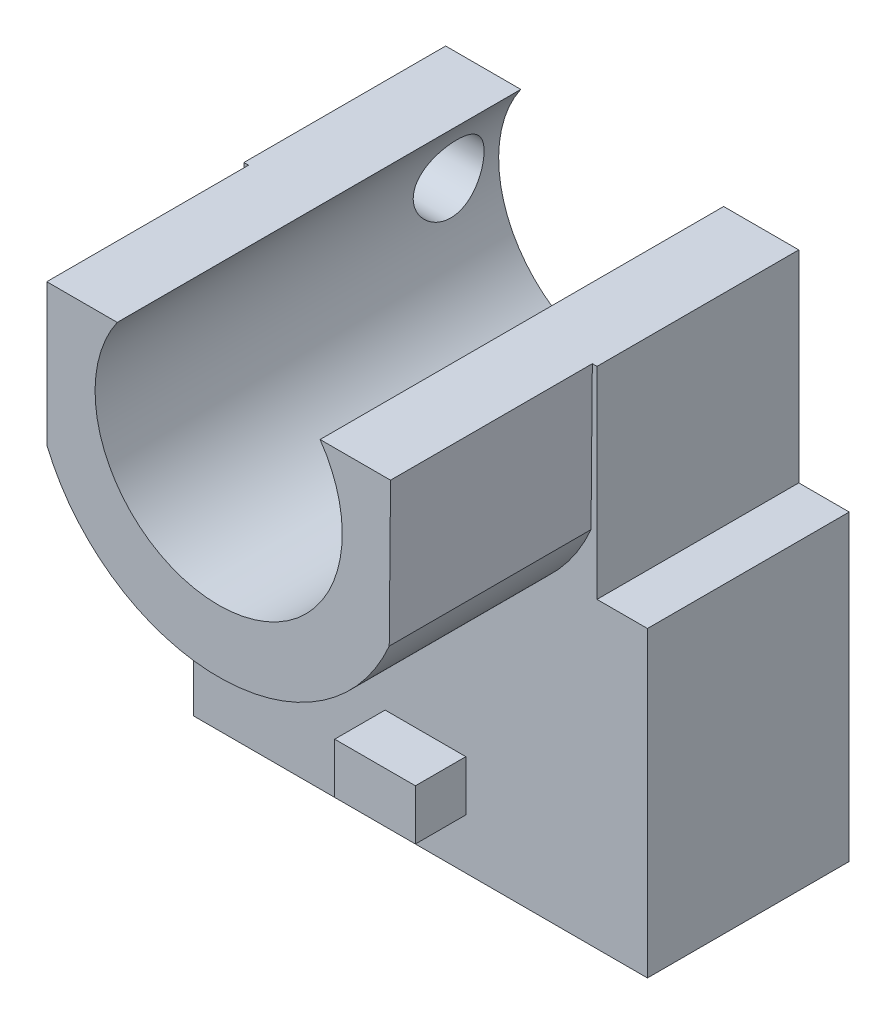
SolidWorks part; units mm, degrees
ref_plane "Front Plane" through (0, 0, 0) normal (0, 0, 1) x (1, 0, 0)
ref_plane "Top Plane" through (0, 0, 0) normal (0, 1, 0) x (1, 0, 0)
ref_plane "Right Plane" through (0, 0, 0) normal (1, 0, 0) x (0, 0, -1)
sketch "Sketch1" plane through (0, 0, 0) normal (0, 0, 1) x (1, 0, 0)
  line L0 (17.5, 15) -> (22.5, 15)
  line L1 (-22.5, -15) -> (22.5, -15)
  line L2 (-22.5, -15) -> (-22.5, 15)
  line L3 (-22.5, 15) -> (-17.5, 15)
  line L4 (22.5, -15) -> (22.5, 15)
  line L5 (-22.5, -15) -> (22.5, 15) construction
  line L6 (-22.5, 15) -> (22.5, -15) construction
  line L8 (-17.5, 15) -> (-17.5, 35)
  line L9 (-17.5, 35) -> (17.5, 35)
  line L10 (17.5, 15) -> (17.5, 35)
  point P0 (0, 0)
  dimension "D1" = 5
  dimension "D2" = 5
  dimension "D3" = 45
  dimension "D4" = 20
  dimension "D5" = 30
extrude "Boss-Extrude1" add sketch "Sketch1" along normal blind 20
sketch "Sketch2" plane through (0, 0, 20) normal (0, 0, 1) x (1, 0, 0)
  line L1 (4.5, -5) -> (-3.5, -5)
  line L2 (4.5, -5) -> (4.5, -10)
  line L3 (4.5, -10) -> (-3.5, -10)
  line L4 (-3.5, -5) -> (-3.5, -10)
  line L5 (4.5, -5) -> (-3.5, -10) construction
  line L6 (4.5, -10) -> (-3.5, -5) construction
  line L7 (-22.5, 15) -> (-22.5, -15) construction
  line L8 (-17.5, 15) -> (-22.5, 15) construction
  point P0 (0.5, -7.5)
  point P9 (-22.5, 0)
  point P12 (-20, 15)
  dimension "D1" = 8
  dimension "D2" = 5
  dimension "D3" = 19
  dimension "D4" = 20
extrude "Boss-Extrude2" add sketch "Sketch2" along normal blind 5 contours L3 L4 L1 L2
sketch "Sketch3" plane through (0, 0, 20) normal (0, 0, 1) x (1, 0, 0)
  line L0 (17.5, 35) -> (-17.5, 35) construction
  line L1 (-17.5, 35) -> (-17.5, 15) construction
  circle A0 centre (0, 28) radius 12.25
  point P4 (0, 35)
  dimension "D1" = 7
  dimension "D2" = 24.5
  dimension "D3" = 17.5
extrude "Cut-Extrude1" cut sketch "Sketch3" against normal blind 20 contours A0
sketch "Sketch4" plane through (0, 0, 20) normal (0, 0, 1) x (1, 0, 0)
  line L0 (-17.0367, 35) -> (-17.0367, 21)
  line L1 (17.0367, 35) -> (10.053, 35) construction
  line L2 (17.5, 35) -> (10.053, 35) construction
  line L3 (-10.053, 35) -> (-17.5, 35) construction
  line L4 (-17.0367, 35) -> (-10.053, 35)
  line L5 (-10.053, 35) -> (-17.0367, 35) construction
  line L6 (10.053, 35) -> (17.0367, 35)
  line L7 (17.0367, 35) -> (16.9066, 20.6913)
  arc A0 (-10.053, 35) -> (10.053, 35) centre (0, 28) ccw
  arc A1 (-17.0367, 21) -> (16.9066, 20.6913) centre (0, 28) ccw
sketch "Sketch5" plane through (0, 35, 0) normal (0, 1, 0) x (1, 0, 0)
extrude "Boss-Extrude3" add sketch "Sketch4" along normal blind 20
sketch "Sketch6" plane through (-17.5, 0, 0) normal (-1, 0, 0) x (0, 0, 1)
  line L0 (20, 35) -> (0, 35) construction
  line L1 (0, 35) -> (0, 15) construction
  circle A0 centre (5, 29) radius 3.5
  dimension "D1" = 7
  dimension "D2" = 6
  dimension "D3" = 5
extrude "Cut-Extrude2" cut sketch "Sketch6" against normal blind 8 and the other way blind 1
